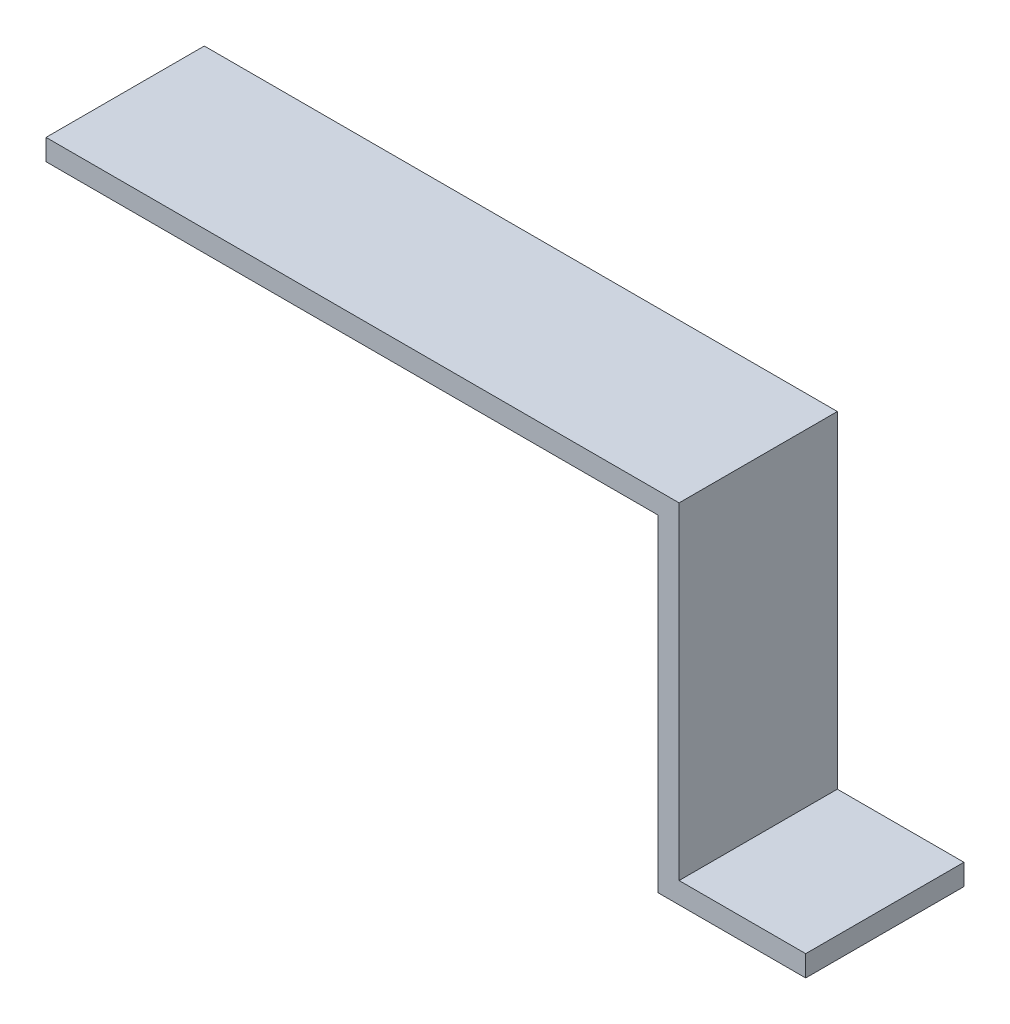
SolidWorks part; units mm, degrees
ref_plane "Ebene vorne" through (0, 0, 0) normal (0, 0, 1) x (1, 0, 0)
ref_plane "Ebene oben" through (0, 0, 0) normal (0, 1, 0) x (1, 0, 0)
ref_plane "Ebene rechts" through (0, 0, 0) normal (1, 0, 0) x (0, 0, -1)
sketch "Skizze2" plane through (0, 0, 0) normal (0, 0, 1) x (1, 0, 0)
  line L0 (0, 0) -> (60, 0)
  line L1 (60, 0) -> (60, -31)
  line L2 (60, -31) -> (84.2396, -31)
  line L3 (84.2396, -31) -> (84.2396, -33)
  line L4 (84.2396, -33) -> (58, -33)
  line L5 (58, -33) -> (58, -2)
  line L6 (58, -2) -> (0, -2)
  line L7 (0, -2) -> (0, 0)
  dimension "D1" = 60
  dimension "D2" = 31
  dimension "D3" = 2
  dimension "D4" = 2
  dimension "D5" = 2
extrude "Aufsatz-Linear austragen1" add sketch "Skizze2" along normal blind 15
sketch "Skizze4" plane through (0, -31, 0) normal (0, 1, 0) x (1, 0, 0)
  line L0 (84.2396, 0) -> (60, 0) construction
  line L1 (84.2396, -15) -> (71.9996, -15)
  line L2 (84.2396, -15) -> (84.2396, 0)
  line L3 (84.2396, 0) -> (71.9996, 0)
  line L4 (71.9996, -15) -> (71.9996, 0)
  dimension "D1" = 12.24
extrude "Schnitt-Linear austragen1" cut sketch "Skizze4" against normal blind 2
